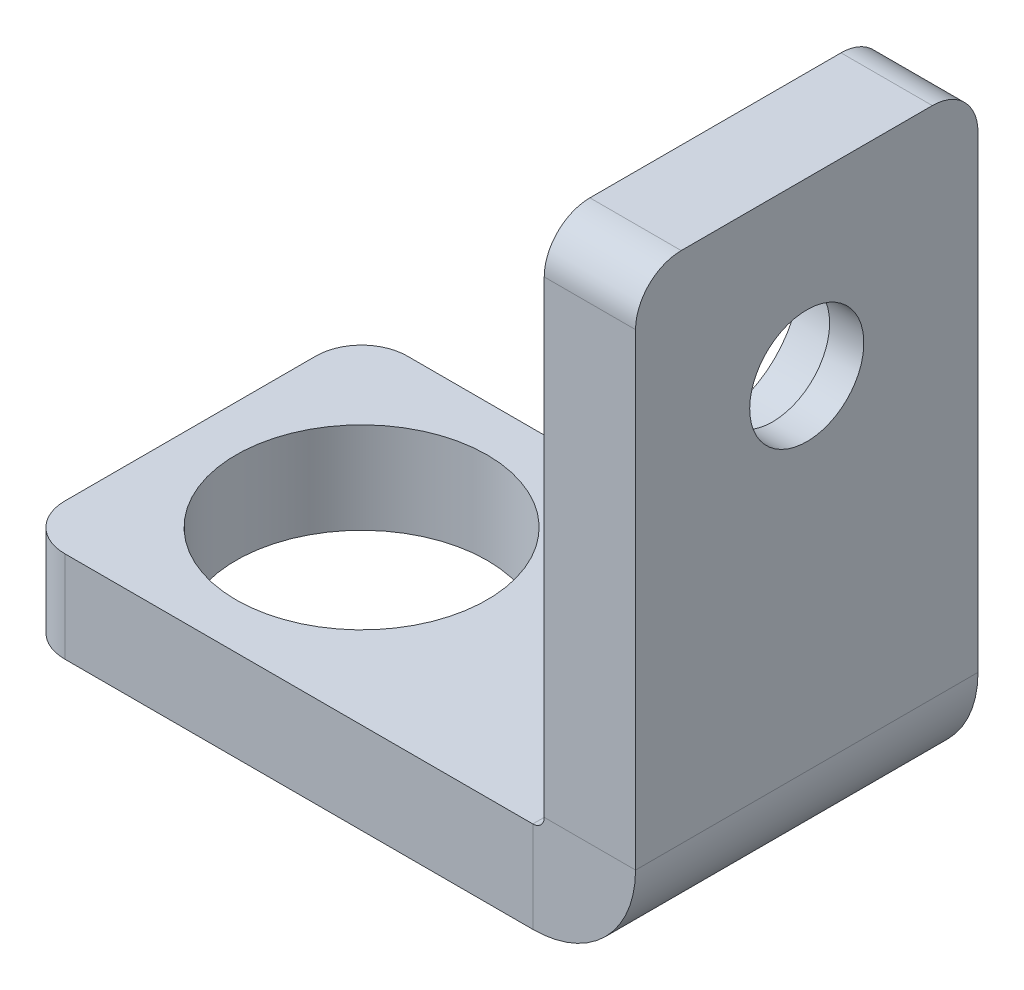
SolidWorks part; units mm, degrees
ref_plane "Front Plane" through (0, 0, 0) normal (0, 0, 1) x (1, 0, 0)
ref_plane "Top Plane" through (0, 0, 0) normal (0, 1, 0) x (1, 0, 0)
ref_plane "Right Plane" through (0, 0, 0) normal (1, 0, 0) x (0, 0, -1)
sketch "Sketch2" plane through (0, 0, 0) normal (0, 0, 1) x (1, 0, 0)
  line L0 (-2.5, 0) -> (-25, 0)
  line L1 (0, 2.5) -> (0, 25)
  arc A0 (-2.5, 0) -> (0, 2.5) centre (-2.5, 2.5) ccw
  point P6 (0, 0)
  dimension "D3" = 2.5
  dimension "D1" = 25
  dimension "D2" = 25
ref_plane "Plane1" through (-25, 0, 0) normal (1, 0, 0) x (0, 0, -1)
sketch "Sketch5" plane through (-25, 0, 0) normal (1, 0, 0) x (0, 0, -1)
  line L1 (-7.5, -2) -> (7.5, -2)
  line L2 (-7.5, -2) -> (-7.5, 2)
  line L3 (-7.5, 2) -> (7.5, 2)
  line L4 (7.5, -2) -> (7.5, 2)
  line L5 (-7.5, -2) -> (7.5, 2) construction
  line L6 (-7.5, 2) -> (7.5, -2) construction
  point P0 (0, 0)
  dimension "D1" = 15
  dimension "D2" = 4
sweep "Sweep1" add profiles "Sketch5" path "Sketch2"
sketch "Sketch6" plane through (0, 2, 0) normal (0, 1, 0) x (1, 0, 0)
  line L2 (-25, -15.9954) -> (-25, 15.9954) construction
  line L4 (-25, 7.5) -> (-2.5, 7.5) construction
  circle A0 centre (-17.5, 0) radius 5.5
  point P4 (-23, 0)
  point P5 (-17.5, 5.5)
  point P6 (0, 0)
  point P8 (0, 0)
  dimension "D1" = 11
  dimension "D2" = 2
  dimension "D3" = 2
extrude "Cut-Extrude1" cut sketch "Sketch6" against normal through all
sketch "Sketch7" plane through (-2, 0, 0) normal (-1, 0, 0) x (0, 0, 1)
  line L1 (-7.5, 25) -> (-7.5, 2.5) construction
  line L2 (-7.5, 2.5) -> (7.5, 2.5) construction
  circle A0 centre (0, 17.5) radius 2.5
  dimension "D1" = 5
  dimension "D2" = 22.5
  dimension "D3" = 15
extrude "Cut-Extrude2" cut sketch "Sketch7" against normal through all
fillet "Fillet1" radius 2 4 edges at (0, 25, -7.5) (0, 25, 7.5) (-25, 0, -7.5) (-25, 0, 7.5)
sketch "Sketch9" plane through (-2, 0, 0) normal (-1, 0, 0) x (0, 0, 1)
  circle A0 centre (0, 17.5) radius 3.7
  dimension "D1" = 7.4
extrude "Cut-Extrude3" cut sketch "Sketch9" against normal offset from surface (2.5 mm away) 1.5 up to face at (2, 17.5, 2.5)
equation "\"D2@Sketch2\"=\"D1@Sketch2\""
equation "\"D2@Sketch6\"=\"D3@Sketch6\""
equation "\"D3@Sketch7\"=\"D2@Sketch7\"*2/3"
